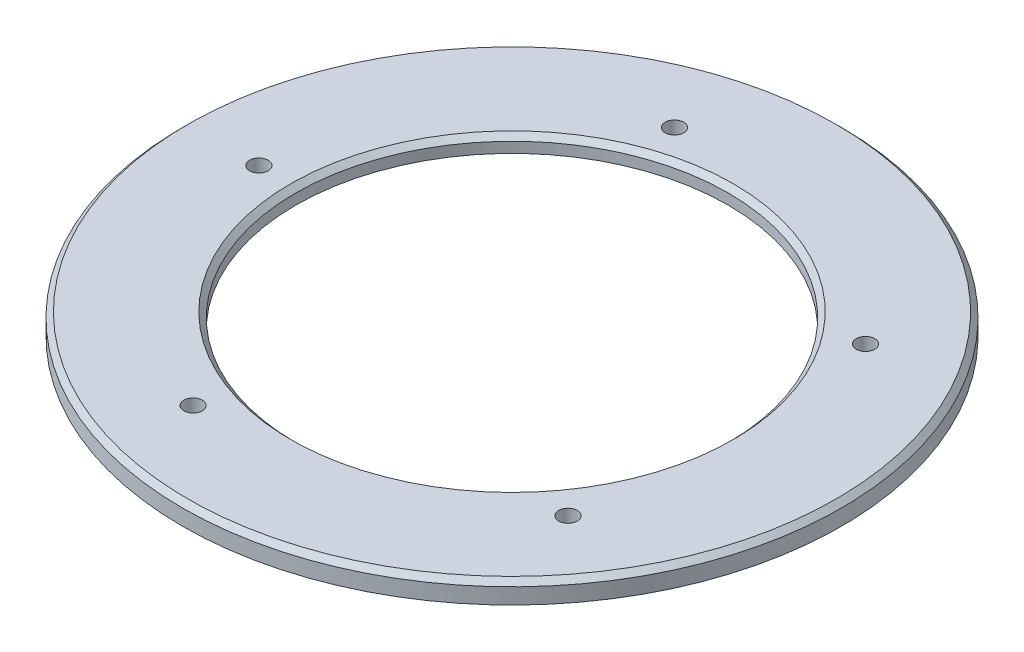
SolidWorks part; units mm, degrees
ref_plane "Front Plane" through (0, 0, 0) normal (0, 0, 1) x (1, 0, 0)
ref_plane "Top Plane" through (0, 0, 0) normal (0, 1, 0) x (1, 0, 0)
ref_plane "Right Plane" through (0, 0, 0) normal (1, 0, 0) x (0, 0, -1)
sketch "Sketch1" plane through (0, 0, 0) normal (0, 0, 1) x (1, 0, 0)
  line L0 (-55, 1) -> (-55, 0)
  line L1 (-55, 0) -> (-62.5, 0)
  line L2 (-62.5, 0) -> (-62.5, 4)
  line L3 (-62.5, 4) -> (-41, 4)
  line L4 (-41, 4) -> (-41, 1)
  line L5 (-41, 1) -> (-55, 1)
  line L6 (0, 0) -> (0, 4.4576) construction
  dimension "D1" = 1
  dimension "D2" = 125
  dimension "D3" = 110
  dimension "D4" = 14
  dimension "D5" = 3
revolve "Revolve1" add sketch "Sketch1" angle 360 about L6
sketch "Sketch2" plane through (0, 1, 0) normal (0, -1, 0) x (1, 0, 0)
  line L0 (-55, 0) -> (-41, 0) construction
  circle A0 centre (-48, 0) radius 1.7521
  circle A1 centre (0, 0) radius 55 construction
  circle A2 centre (0, 0) radius 41 construction
  circle A3 centre (-14.8328, 45.6507) radius 1.7521
  circle A4 centre (38.8328, 28.2137) radius 1.7521
  circle A5 centre (38.8328, -28.2137) radius 1.7521
  circle A6 centre (-14.8328, -45.6507) radius 1.7521
  point P9 (-48, 0)
  point P10 (0, 0)
  point P17 (0, 0)
  point P20 (0, 0)
  point P23 (0, 0)
  point P26 (0, 0)
  point P27 (0, 0)
  dimension "D1" = 3.5042
  dimension "D2" = 5
extrude "Cut-Extrude2" cut sketch "Sketch2" against normal through all
chamfer "Chamfer1" distance 1 angle 45 2 edges at (0, 4, -62.5) (0, 4, -41)
